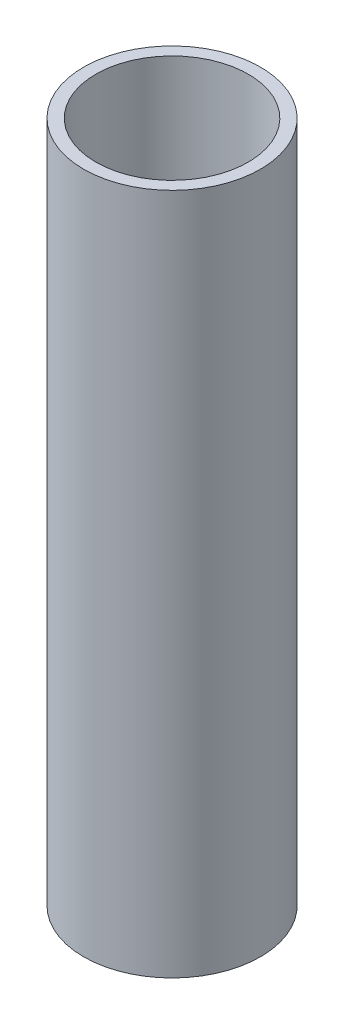
SolidWorks part; units mm, degrees
material "PVC Rigid"
ref_plane "Front Plane" through (0, 0, 0) normal (0, 0, 1) x (1, 0, 0)
ref_plane "Top Plane" through (0, 0, 0) normal (0, 1, 0) x (1, 0, 0)
ref_plane "Right Plane" through (0, 0, 0) normal (1, 0, 0) x (0, 0, -1)
sketch "Sketch2" plane through (0, 0, 0) normal (0, 1, 0) x (1, 0, 0)
  circle A0 centre (0, 0) radius 30.1625
  circle A1 centre (0, 0) radius 25.9969
  dimension "D1" = 60.325
  dimension "D2" = 51.9938
extrude "Boss-Extrude1" add sketch "Sketch2" along normal blind 232.625
